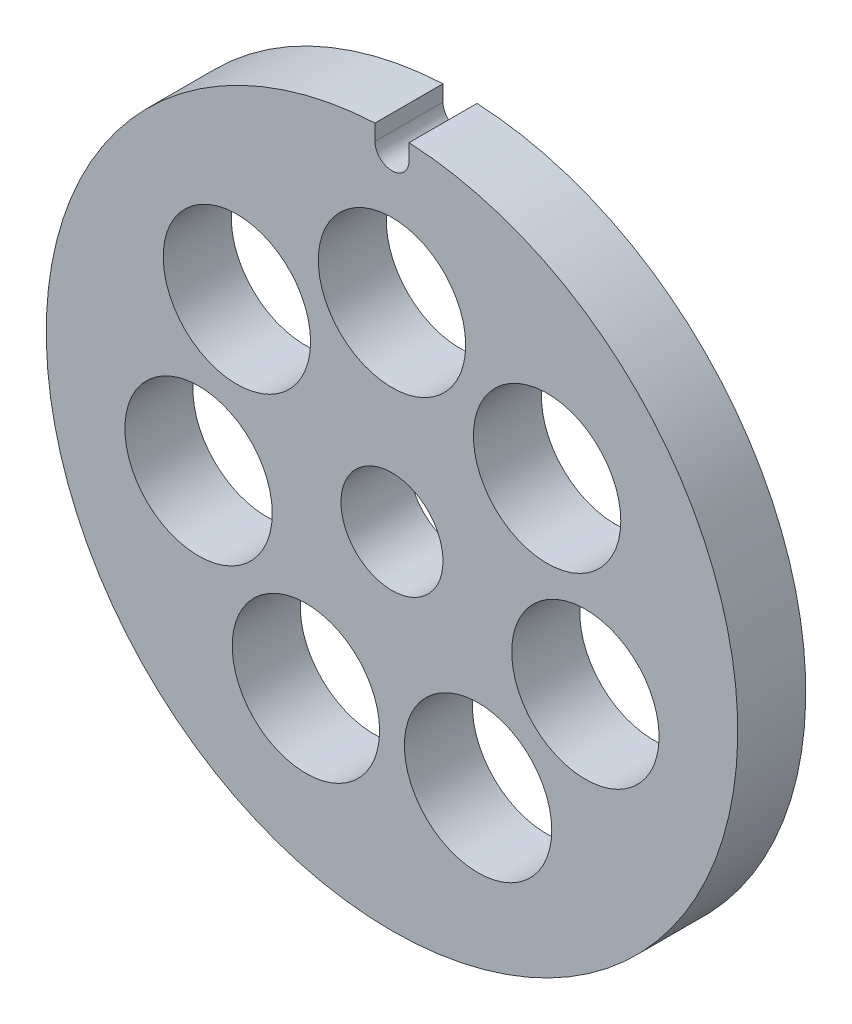
SolidWorks part; units mm, degrees
ref_plane "Płaszczyzna przednia" through (0, 0, 0) normal (0, 0, 1) x (1, 0, 0)
ref_plane "Płaszczyzna górna" through (0, 0, 0) normal (0, 1, 0) x (1, 0, 0)
ref_plane "Płaszczyzna prawa" through (0, 0, 0) normal (1, 0, 0) x (0, 0, -1)
sketch "Szkic1" plane through (0, 0, 0) normal (0, 0, 1) x (1, 0, 0)
  line L0 (-1.5, 29.0631) -> (-1.5, 30.4631)
  line L1 (1.5, 29.0631) -> (1.5, 30.4631)
  arc A0 (-1.5, 30.4631) -> (1.5, 30.4631) centre (0, 0) ccw
  circle A1 centre (0, 0) radius 4.5
  circle A2 centre (0, 17.5) radius 6.5
  circle A3 centre (13.6821, 10.9111) radius 6.5
  circle A4 centre (17.0612, -3.8941) radius 6.5
  circle A5 centre (7.593, -15.767) radius 6.5
  circle A6 centre (-7.593, -15.767) radius 6.5
  circle A7 centre (-17.0612, -3.8941) radius 6.5
  circle A8 centre (-13.6821, 10.9111) radius 6.5
  arc A9 (-1.5, 29.0631) -> (1.5, 29.0631) centre (0, 29.0631) ccw
  point P1 (0, 0)
  point P25 (0, 0)
  dimension "D1" = 9
  dimension "D2" = 13
  dimension "D4" = 61
  dimension "D6" = 3
  dimension "D3" = 17.5
  dimension "D7" = 1.4
  dimension "D5" = 7
extrude "Dodanie-wyciągnięcie1" add sketch "Szkic1" along normal blind 6
